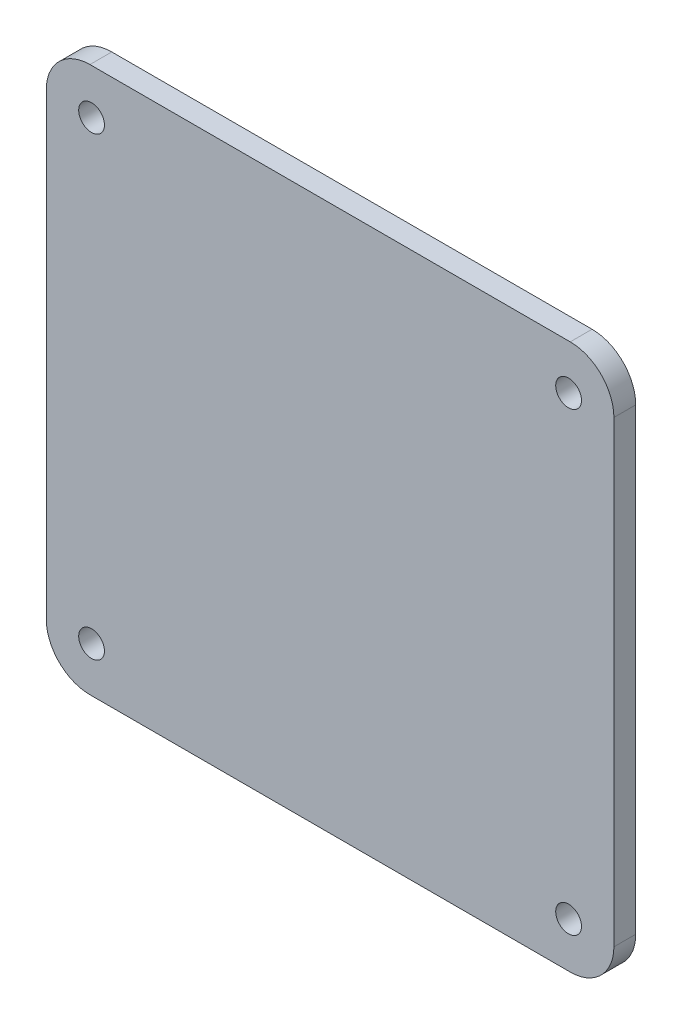
SolidWorks part; units mm, degrees
ref_plane "Front Plane" through (0, 0, 0) normal (0, 0, 1) x (1, 0, 0)
ref_plane "Top Plane" through (0, 0, 0) normal (0, 1, 0) x (1, 0, 0)
ref_plane "Right Plane" through (0, 0, 0) normal (1, 0, 0) x (0, 0, -1)
sketch "Sketch1" plane through (0, 0, 0) normal (0, 0, 1) x (1, 0, 0)
  line L1 (-27.94, -31.75) -> (27.94, -31.75)
  line L2 (-33.02, -26.67) -> (-33.02, 26.67)
  line L3 (-27.94, 31.75) -> (27.94, 31.75)
  line L4 (33.02, -26.67) -> (33.02, 26.67)
  line L5 (-33.02, -31.75) -> (33.02, 31.75) construction
  line L6 (-33.02, 31.75) -> (33.02, -31.75) construction
  arc A0 (-27.94, -31.75) -> (-33.02, -26.67) centre (-27.94, -26.67) cw
  arc A1 (27.94, -31.75) -> (33.02, -26.67) centre (27.94, -26.67) ccw
  arc A2 (27.94, 31.75) -> (33.02, 26.67) centre (27.94, 26.67) cw
  arc A3 (-33.02, 26.67) -> (-27.94, 31.75) centre (-27.94, 26.67) cw
  point P0 (0, 0)
  dimension "D3" = 5.08
  dimension "D1" = 66.04
  dimension "D2" = 63.5
extrude "Boss-Extrude1" add sketch "Sketch1" along normal blind 2.54
sketch "Sketch2" plane through (0, 0, 2.54) normal (0, 0, 1) x (1, 0, 0)
  line L1 (-27.75, -26.5) -> (27.75, -26.5) construction
  line L2 (-27.75, -26.5) -> (-27.75, 26.5) construction
  line L3 (-27.75, 26.5) -> (27.75, 26.5) construction
  line L4 (27.75, -26.5) -> (27.75, 26.5) construction
  line L5 (-27.75, -26.5) -> (27.75, 26.5) construction
  line L6 (-27.75, 26.5) -> (27.75, -26.5) construction
  circle A0 centre (-27.75, 26.5) radius 1.5
  circle A1 centre (27.75, 26.5) radius 1.5
  circle A2 centre (-27.75, -26.5) radius 1.5
  circle A3 centre (27.75, -26.5) radius 1.5
  point P0 (0, 0)
  dimension "D3" = 3
  dimension "D4" = 3
  dimension "D5" = 3
  dimension "D6" = 3
  dimension "D1" = 55.5
  dimension "D2" = 53
extrude "Cut-Extrude1" cut sketch "Sketch2" against normal through all
